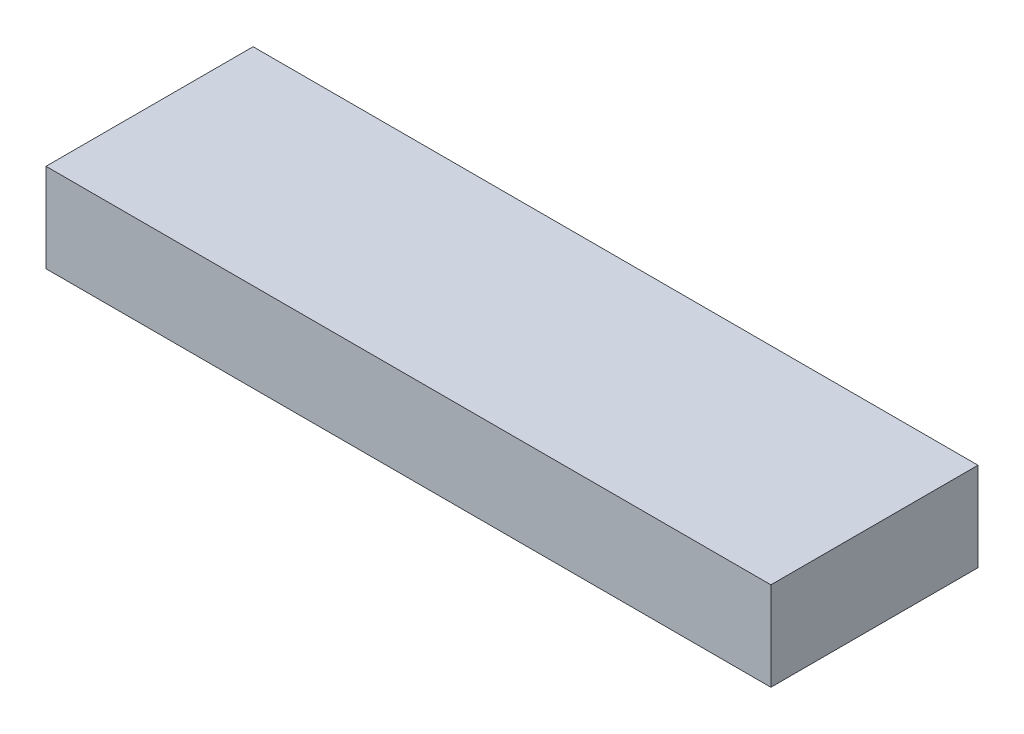
SolidWorks part; units mm, degrees
ref_plane "Front Plane" through (0, 0, 0) normal (0, 0, 1) x (1, 0, 0)
ref_plane "Top Plane" through (0, 0, 0) normal (0, 1, 0) x (1, 0, 0)
ref_plane "Right Plane" through (0, 0, 0) normal (1, 0, 0) x (0, 0, -1)
sketch "Sketch1" plane through (0, 0, 0) normal (0, 1, 0) x (1, 0, 0)
  line L1 (0, 0) -> (311.15, 0)
  line L2 (0, 0) -> (0, -88.9)
  line L3 (0, -88.9) -> (311.15, -88.9)
  line L4 (311.15, 0) -> (311.15, -88.9)
extrude "Boss-Extrude1" add sketch "Sketch1" along normal blind 38.1
sketch "Sketch2" plane through (0, 38.1, 0) normal (0, 1, 0) x (1, 0, 0)
  line L0 (0, -44.45) -> (103.7167, -44.45) construction
  line L1 (0, 0) -> (0, -88.9) construction
  line L2 (103.7167, -44.45) -> (207.4333, -44.45) construction
  line L3 (207.4333, -44.45) -> (311.15, -44.45) construction
  line L4 (311.15, -88.9) -> (311.15, 0) construction
  line L5 (103.7167, 0) -> (103.7167, -88.9) construction
  line L6 (311.15, 0) -> (0, 0) construction
  line L7 (0, -88.9) -> (311.15, -88.9) construction
  line L8 (207.4333, 0) -> (207.4333, -88.9) construction
sketch "Sketch3" plane through (0, 0, 0) normal (0, -1, 0) x (1, 0, 0)
  line L0 (0, 44.45) -> (103.7167, 44.45) construction
  line L1 (103.7167, 44.45) -> (207.4333, 44.45) construction
  line L2 (207.4333, 44.45) -> (311.15, 44.45) construction
  line L3 (103.7167, 88.9) -> (103.7167, 0) construction
  line L4 (207.4333, 88.9) -> (207.4333, 0) construction
